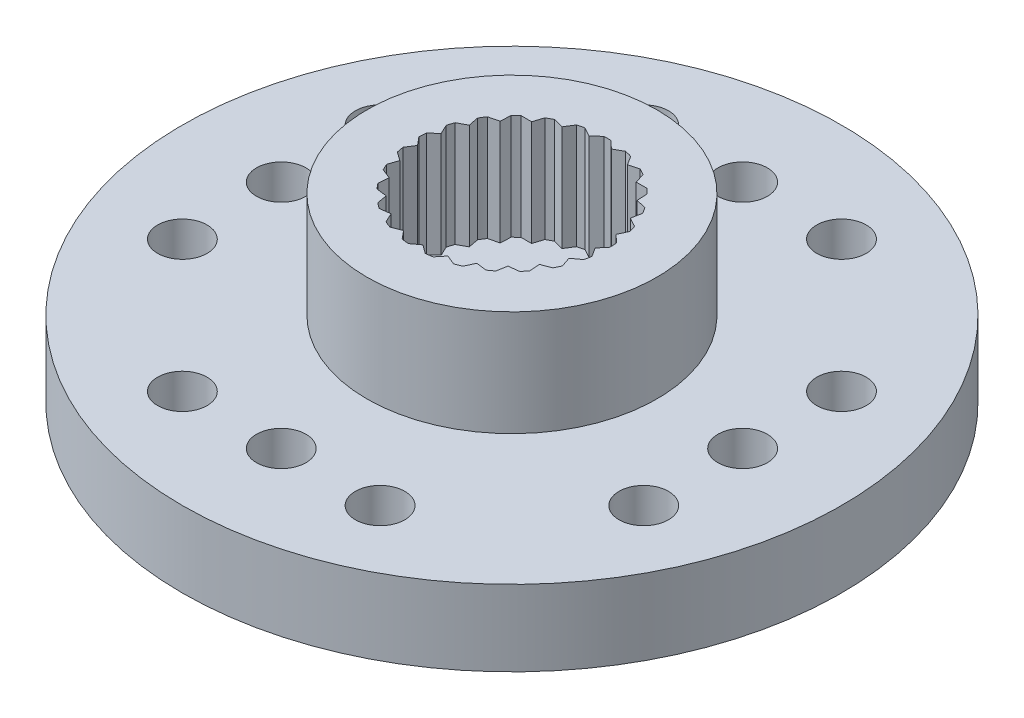
SolidWorks part; units mm, degrees
material "ABS"
ref_plane "Front Plane" through (0, 0, 0) normal (0, 0, 1) x (1, 0, 0)
ref_plane "Top Plane" through (0, 0, 0) normal (0, 1, 0) x (1, 0, 0)
ref_plane "Right Plane" through (0, 0, 0) normal (1, 0, 0) x (0, 0, -1)
sketch "Sketch2" plane through (0, 0, 0) normal (0, 1, 0) x (1, 0, 0)
  circle A0 centre (0, 0) radius 6
  circle A1 centre (0, 0) radius 1.5
  dimension "D1" = 12
  dimension "D2" = 3
extrude "Boss-Extrude1" add sketch "Sketch2" along normal mid plane 2.3
sketch "Sketch3" plane through (0, 1.15, 0) normal (0, 1, 0) x (1, 0, 0)
  line L0 (0, 0) -> (0, 2.9) construction
  line L3 (0, 0) -> (0.376, 2.9763) construction
  line L52 (0.1074, 2.898) -> (0.3384, 2.6787)
  line L53 (-0.1074, 2.898) -> (-0.3384, 2.6787)
  line L54 (0.8248, 2.7802) -> (0.9939, 2.5104)
  line L55 (0.6167, 2.8337) -> (0.3384, 2.6787)
  line L56 (1.4903, 2.4878) -> (1.587, 2.1843)
  line L57 (1.302, 2.5913) -> (0.9939, 2.5104)
  line L58 (2.0621, 2.039) -> (2.0804, 1.721)
  line L59 (1.9055, 2.1861) -> (1.587, 2.1843)
  line L60 (2.5044, 1.4621) -> (2.443, 1.1496)
  line L61 (2.3893, 1.6435) -> (2.0804, 1.721)
  line L62 (2.7894, 0.7934) -> (2.6522, 0.5059)
  line L63 (2.723, 0.9977) -> (2.443, 1.1496)
  line L64 (2.899, 0.0748) -> (2.6947, -0.1695)
  line L65 (2.8855, 0.2892) -> (2.6522, 0.5059)
  line L66 (2.8265, -0.6486) -> (2.5679, -0.8343)
  line L67 (2.8668, -0.4375) -> (2.6947, -0.1695)
  line L68 (2.5765, -1.3311) -> (2.2797, -1.4467)
  line L69 (2.6679, -1.1367) -> (2.5679, -0.8343)
  line L70 (2.1645, -1.93) -> (1.8483, -1.9682)
  line L71 (2.3014, -1.7645) -> (2.2797, -1.4467)
  line L72 (1.6165, -2.4077) -> (1.3007, -2.366)
  line L73 (1.7903, -2.2814) -> (1.8483, -1.9682)
  line L74 (0.967, -2.734) -> (0.6715, -2.6152)
  line L75 (1.1667, -2.655) -> (1.3007, -2.366)
  line L76 (0.2566, -2.8886) -> (0, -2.7)
  line L77 (0.4698, -2.8617) -> (0.6715, -2.6152)
  line L78 (-0.4698, -2.8617) -> (-0.6715, -2.6152)
  line L79 (-0.2566, -2.8886) -> (0, -2.7)
  line L80 (-1.1667, -2.655) -> (-1.3007, -2.366)
  line L81 (-0.967, -2.734) -> (-0.6715, -2.6152)
  line L82 (-1.7903, -2.2814) -> (-1.8483, -1.9682)
  line L83 (-1.6165, -2.4077) -> (-1.3007, -2.366)
  line L84 (-2.3014, -1.7645) -> (-2.2797, -1.4467)
  line L85 (-2.1645, -1.93) -> (-1.8483, -1.9682)
  line L86 (-2.6679, -1.1367) -> (-2.5679, -0.8343)
  line L87 (-2.5765, -1.3311) -> (-2.2797, -1.4467)
  line L88 (-2.8668, -0.4375) -> (-2.6947, -0.1695)
  line L89 (-2.8265, -0.6486) -> (-2.5679, -0.8343)
  line L90 (-2.8855, 0.2892) -> (-2.6522, 0.5059)
  line L91 (-2.899, 0.0748) -> (-2.6947, -0.1695)
  line L92 (-2.723, 0.9977) -> (-2.443, 1.1496)
  line L93 (-2.7894, 0.7934) -> (-2.6522, 0.5059)
  line L94 (-2.3893, 1.6435) -> (-2.0804, 1.721)
  line L95 (-2.5044, 1.4621) -> (-2.443, 1.1496)
  line L96 (-1.9055, 2.1861) -> (-1.587, 2.1843)
  line L97 (-2.0621, 2.039) -> (-2.0804, 1.721)
  line L98 (-1.302, 2.5913) -> (-0.9939, 2.5104)
  line L99 (-1.4903, 2.4878) -> (-1.587, 2.1843)
  line L100 (-0.6167, 2.8337) -> (-0.3384, 2.6787)
  line L101 (-0.8248, 2.7802) -> (-0.9939, 2.5104)
  line L102 (-2.533, 1.6075) -> (-2.3893, 1.6435) construction
  line L103 (-2.533, 1.6075) -> (-2.5044, 1.4621) construction
  line L104 (-2.8532, 0.9271) -> (-2.723, 0.9977) construction
  line L105 (-2.8532, 0.9271) -> (-2.7894, 0.7934) construction
  line L106 (-2.9941, 0.1884) -> (-2.8855, 0.2892) construction
  line L107 (-2.9941, 0.1884) -> (-2.899, 0.0748) construction
  line L108 (-2.9469, -0.5621) -> (-2.8668, -0.4375) construction
  line L109 (-2.9469, -0.5621) -> (-2.8265, -0.6486) construction
  line L110 (0, 3) -> (0.1074, 2.898) construction
  line L111 (0, 2.9) -> (0, 3) construction
  line L112 (0, 3) -> (-0.1074, 2.898) construction
  line L113 (-0.7461, 2.9057) -> (-0.6167, 2.8337) construction
  line L114 (-0.7461, 2.9057) -> (-0.8248, 2.7802) construction
  line L115 (-1.4453, 2.6289) -> (-1.302, 2.5913) construction
  line L116 (-1.4453, 2.6289) -> (-1.4903, 2.4878) construction
  line L117 (-2.0536, 2.1869) -> (-1.9055, 2.1861) construction
  line L118 (-2.0536, 2.1869) -> (-2.0621, 2.039) construction
  line L119 (-2.7145, -1.2773) -> (-2.6679, -1.1367) construction
  line L120 (-2.7145, -1.2773) -> (-2.5765, -1.3311) construction
  line L121 (-2.3115, -1.9123) -> (-2.3014, -1.7645) construction
  line L122 (-2.3115, -1.9123) -> (-2.1645, -1.93) construction
  line L123 (-1.7634, -2.4271) -> (-1.7903, -2.2814) construction
  line L124 (-1.7634, -2.4271) -> (-1.6165, -2.4077) construction
  line L125 (-1.1044, -2.7893) -> (-1.1667, -2.655) construction
  line L126 (-1.1044, -2.7893) -> (-0.967, -2.734) construction
  line L127 (-0.376, -2.9763) -> (-0.4698, -2.8617) construction
  line L128 (-0.376, -2.9763) -> (-0.2566, -2.8886) construction
  line L129 (0.376, -2.9763) -> (0.2566, -2.8886) construction
  line L130 (0.376, -2.9763) -> (0.4698, -2.8617) construction
  line L131 (1.1044, -2.7893) -> (0.967, -2.734) construction
  line L132 (1.1044, -2.7893) -> (1.1667, -2.655) construction
  line L133 (1.7634, -2.4271) -> (1.6165, -2.4077) construction
  line L134 (1.7634, -2.4271) -> (1.7903, -2.2814) construction
  line L135 (2.3115, -1.9123) -> (2.3014, -1.7645) construction
  line L136 (2.3115, -1.9123) -> (2.1645, -1.93) construction
  line L137 (2.7145, -1.2773) -> (2.6679, -1.1367) construction
  line L138 (2.7145, -1.2773) -> (2.5765, -1.3311) construction
  line L139 (2.9469, -0.5621) -> (2.8668, -0.4375) construction
  line L140 (2.9469, -0.5621) -> (2.8265, -0.6486) construction
  line L141 (2.9941, 0.1884) -> (2.8855, 0.2892) construction
  line L142 (2.9941, 0.1884) -> (2.899, 0.0748) construction
  line L143 (2.8532, 0.9271) -> (2.723, 0.9977) construction
  line L144 (2.8532, 0.9271) -> (2.7894, 0.7934) construction
  line L145 (2.533, 1.6075) -> (2.3893, 1.6435) construction
  line L146 (2.533, 1.6075) -> (2.5044, 1.4621) construction
  line L147 (2.0536, 2.1869) -> (1.9055, 2.1861) construction
  line L148 (2.0536, 2.1869) -> (2.0621, 2.039) construction
  line L149 (1.4453, 2.6289) -> (1.302, 2.5913) construction
  line L150 (1.4453, 2.6289) -> (1.4903, 2.4878) construction
  line L151 (0.7461, 2.9057) -> (0.6167, 2.8337) construction
  line L152 (0.7461, 2.9057) -> (0.8248, 2.7802) construction
  circle A0 centre (0, 0) radius 4.4
  circle A1 centre (0, 0) radius 3 construction
  circle A2 centre (0, 0) radius 2.7 construction
  arc A3 (-0.6167, 2.8337) -> (-0.8248, 2.7802) centre (0, 0) ccw
  arc A4 (-0.1074, 2.898) -> (-0.6167, 2.8337) centre (0, 0) ccw construction
  arc A5 (-0.8248, 2.7802) -> (-1.302, 2.5913) centre (0, 0) ccw construction
  arc A6 (-1.302, 2.5913) -> (-1.4903, 2.4878) centre (0, 0) ccw
  arc A7 (-1.4903, 2.4878) -> (-1.9055, 2.1861) centre (0, 0) ccw construction
  arc A8 (-1.9055, 2.1861) -> (-2.0621, 2.039) centre (0, 0) ccw
  arc A9 (-2.0621, 2.039) -> (-2.3893, 1.6435) centre (0, 0) ccw construction
  arc A10 (-2.3893, 1.6435) -> (-2.5044, 1.4621) centre (0, 0) ccw
  arc A11 (-2.5044, 1.4621) -> (-2.723, 0.9977) centre (0, 0) ccw construction
  arc A12 (-2.723, 0.9977) -> (-2.7894, 0.7934) centre (0, 0) ccw
  arc A13 (-2.7894, 0.7934) -> (-2.8855, 0.2892) centre (0, 0) ccw construction
  arc A14 (-2.8855, 0.2892) -> (-2.899, 0.0748) centre (0, 0) ccw
  arc A15 (-2.899, 0.0748) -> (-2.8668, -0.4375) centre (0, 0) ccw construction
  arc A16 (-2.8668, -0.4375) -> (-2.8265, -0.6486) centre (0, 0) ccw
  arc A17 (-2.8265, -0.6486) -> (-2.6679, -1.1367) centre (0, 0) ccw construction
  arc A18 (-2.6679, -1.1367) -> (-2.5765, -1.3311) centre (0, 0) ccw
  arc A19 (-2.5765, -1.3311) -> (-2.3014, -1.7645) centre (0, 0) ccw construction
  arc A20 (-2.3014, -1.7645) -> (-2.1645, -1.93) centre (0, 0) ccw
  arc A21 (-2.1645, -1.93) -> (-1.7903, -2.2814) centre (0, 0) ccw construction
  arc A22 (-1.7903, -2.2814) -> (-1.6165, -2.4077) centre (0, 0) ccw
  arc A23 (-1.6165, -2.4077) -> (-1.1667, -2.655) centre (0, 0) ccw construction
  arc A24 (-1.1667, -2.655) -> (-0.967, -2.734) centre (0, 0) ccw
  arc A25 (-0.967, -2.734) -> (-0.4698, -2.8617) centre (0, 0) ccw construction
  arc A26 (-0.4698, -2.8617) -> (-0.2566, -2.8886) centre (0, 0) ccw
  arc A27 (-0.2566, -2.8886) -> (0.2566, -2.8886) centre (0, 0) ccw construction
  arc A28 (0.2566, -2.8886) -> (0.4698, -2.8617) centre (0, 0) ccw
  arc A29 (0.4698, -2.8617) -> (0.967, -2.734) centre (0, 0) ccw construction
  arc A30 (0.967, -2.734) -> (1.1667, -2.655) centre (0, 0) ccw
  arc A31 (1.1667, -2.655) -> (1.6165, -2.4077) centre (0, 0) ccw construction
  arc A32 (1.6165, -2.4077) -> (1.7903, -2.2814) centre (0, 0) ccw
  arc A33 (1.7903, -2.2814) -> (2.1645, -1.93) centre (0, 0) ccw construction
  arc A34 (2.1645, -1.93) -> (2.3014, -1.7645) centre (0, 0) ccw
  arc A35 (2.3014, -1.7645) -> (2.5765, -1.3311) centre (0, 0) ccw construction
  arc A36 (2.5765, -1.3311) -> (2.6679, -1.1367) centre (0, 0) ccw
  arc A37 (2.6679, -1.1367) -> (2.8265, -0.6486) centre (0, 0) ccw construction
  arc A38 (2.8265, -0.6486) -> (2.8668, -0.4375) centre (0, 0) ccw
  arc A39 (2.8668, -0.4375) -> (2.899, 0.0748) centre (0, 0) ccw construction
  arc A40 (2.899, 0.0748) -> (2.8855, 0.2892) centre (0, 0) ccw
  arc A41 (2.8855, 0.2892) -> (2.7894, 0.7934) centre (0, 0) ccw construction
  arc A42 (2.7894, 0.7934) -> (2.723, 0.9977) centre (0, 0) ccw
  arc A43 (2.723, 0.9977) -> (2.5044, 1.4621) centre (0, 0) ccw construction
  arc A44 (2.5044, 1.4621) -> (2.3893, 1.6435) centre (0, 0) ccw
  arc A45 (2.3893, 1.6435) -> (2.0621, 2.039) centre (0, 0) ccw construction
  arc A46 (2.0621, 2.039) -> (1.9055, 2.1861) centre (0, 0) ccw
  arc A47 (1.9055, 2.1861) -> (1.4903, 2.4878) centre (0, 0) ccw construction
  arc A48 (1.4903, 2.4878) -> (1.302, 2.5913) centre (0, 0) ccw
  arc A49 (1.302, 2.5913) -> (0.8248, 2.7802) centre (0, 0) ccw construction
  arc A50 (0.8248, 2.7802) -> (0.6167, 2.8337) centre (0, 0) ccw
  arc A51 (0.3635, 2.8771) -> (0.1074, 2.898) centre (0, 0) ccw construction
  arc A52 (0.1074, 2.898) -> (-0.1074, 2.898) centre (0, 0) ccw
  arc A53 (0.6167, 2.8337) -> (0.3635, 2.8771) centre (0, 0) ccw construction
  point P84 (0, 0)
  dimension "D1" = 8.8
  dimension "D2" = 5.4
  dimension "D3" = 6
  dimension "D6" = 5.8
  dimension "D4" = 7.2
  dimension "D5" = 25
extrude "Boss-Extrude2" add sketch "Sketch3" along normal blind 3.2
sketch "Sketch4" plane through (0, 0, 0) normal (0, 1, 0) x (1, 0, 0)
  line L0 (0, 0) -> (13, 0) construction
  line L1 (3.9686, 4.5) -> (14.0007, 2.4494)
  line L2 (3.9686, -4.5) -> (14.0007, -2.4494)
  line L3 (13, 0) -> (10, 0) construction
  circle A0 centre (0, 0) radius 6 construction
  arc A1 (3.9686, -4.5) -> (3.9686, 4.5) centre (0, 0) ccw
  arc A2 (14.0007, 2.4494) -> (14.0007, -2.4494) centre (13.5, 0) cw
  circle A3 centre (13, 0) radius 0.75
  circle A4 centre (10, 0) radius 0.75
  circle A5 centre (7, 0) radius 0.75
  dimension "D3" = 2.5
  dimension "D5" = 1.5
  dimension "D2" = 9
  dimension "D7" = 3
  dimension "D4" = 0.5
  dimension "D1" = 13
  dimension "D6" = 3
extrude "Boss-Extrude3" [suppressed] add sketch "Sketch4" along normal mid plane 2.3
pattern_circular "CirPattern1" [suppressed] count 6 over 360
sketch "Sketch5" plane through (0, 0, 0) normal (0, 1, 0) x (1, 0, 0)
  line L0 (3, 7) -> (-3, 7) construction
  circle A0 centre (0, 0) radius 10
  circle A1 centre (0, 7) radius 0.75
  circle A2 centre (-3, 7) radius 0.75
  circle A3 centre (3, 7) radius 0.75
  circle A4 centre (7, 3) radius 0.75
  circle A5 centre (7, 0) radius 0.75
  circle A6 centre (7, -3) radius 0.75
  circle A7 centre (3, -7) radius 0.75
  circle A8 centre (0, -7) radius 0.75
  circle A9 centre (-3, -7) radius 0.75
  circle A10 centre (-7, -3) radius 0.75
  circle A11 centre (-7, 0) radius 0.75
  circle A12 centre (-7, 3) radius 0.75
  circle A13 centre (0, 0) radius 1.5 construction
  circle A14 centre (0, 0) radius 1.5
  point P8 (0, 7)
  point P31 (0, 0)
  dimension "D1" = 1.5
  dimension "D3" = 2.25
  dimension "D4" = 6
  dimension "D2" = 7
  dimension "D5" = 4
extrude "Boss-Extrude4" add sketch "Sketch5" along normal mid plane 2.3
equation "\"N_hole\"= 3"
equation "\"N_horn\"= 6"
equation "\"D6@Sketch4\"=\"N_hole\""
equation "\"D1@CirPattern1\"=\"N_horn\""
equation "\"D1@Sketch4\"=(\"N_hole\" - 1) *3 +7"
